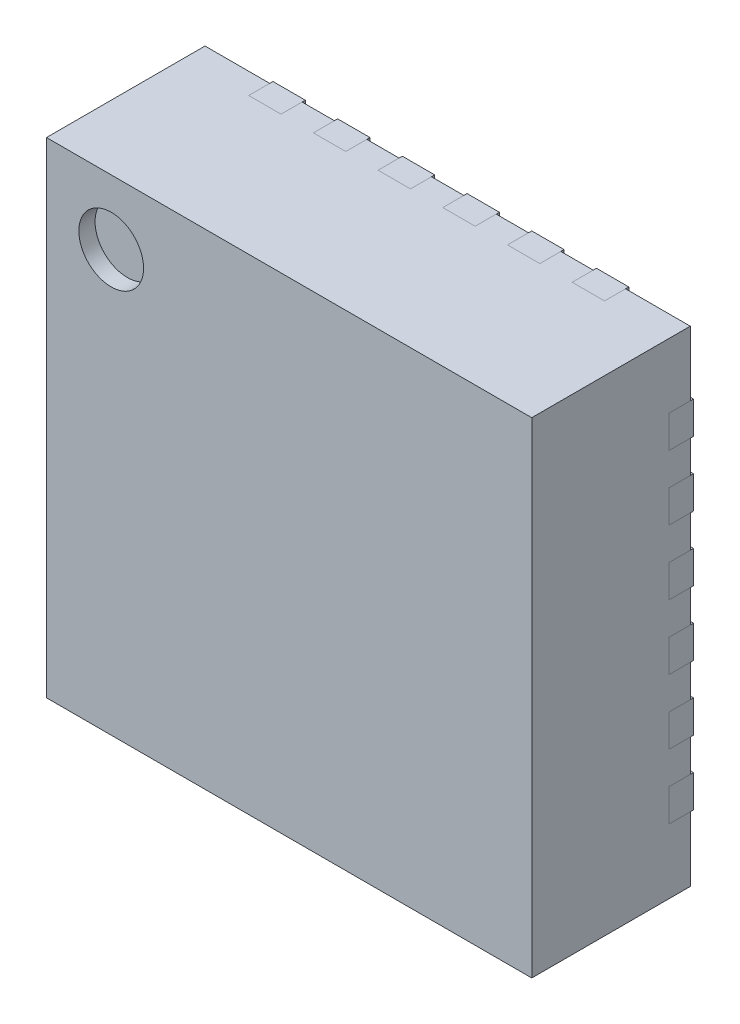
SolidWorks part; units mm, degrees
ref_plane "Plan de face" through (0, 0, 0) normal (0, 0, 1) x (1, 0, 0)
ref_plane "Plan de dessus" through (0, 0, 0) normal (0, 1, 0) x (1, 0, 0)
ref_plane "Plan de droite" through (0, 0, 0) normal (1, 0, 0) x (0, 0, -1)
sketch "Esquisse1" plane through (0, 0, 0) normal (0, 0, 1) x (1, 0, 0)
  line L1 (-1.5, 1.5) -> (1.5, 1.5)
  line L2 (-1.5, 1.5) -> (-1.5, -1.5)
  line L3 (-1.5, -1.5) -> (1.5, -1.5)
  line L4 (1.5, 1.5) -> (1.5, -1.5)
  line L5 (-1.5, 1.5) -> (1.5, -1.5) construction
  line L6 (-1.5, -1.5) -> (1.5, 1.5) construction
  point P0 (0, 0)
  dimension "D1" = 3
  dimension "D2" = 3
extrude "Boss.-Extru.1" add sketch "Esquisse1" along normal blind 0.98
sketch "Esquisse3" plane through (0, 0, 0) normal (0, 0, 1) x (1, 0, 0)
  line L0 (-1.275, -0.5) -> (-1.5, -0.5)
  line L1 (-1.5, -0.5) -> (-1.5, -0.7)
  line L2 (-1.7498, -0.6) -> (-1.1482, -0.6) construction
  line L4 (-1.5, 1.5) -> (-1.5, -1.5) construction
  line L5 (-1.2, -0.575) -> (-1.2, -0.625)
  line L9 (0.85, 0.62) -> (0.85, -0.62)
  line L10 (0.7, -0.77) -> (-0.7, -0.77)
  line L12 (1.8846, 0) -> (-2.1932, 0) construction
  line L13 (-1.5, 1.1) -> (-1.28, 1.1)
  line L26 (-1.7498, -1) -> (-1.1482, -1) construction
  line L60 (-1.5, -0.7) -> (-1.275, -0.7)
  line L77 (-1.5, -0.1) -> (-1.5, -0.3)
  line L78 (-0.6, 0.77) -> (-0.85, 0.52)
  line L79 (0.7, 0.77) -> (-0.6, 0.77)
  line L80 (-0.85, 0.52) -> (-0.85, -0.62)
  line L81 (-1.5, -0.3) -> (-1.275, -0.3)
  line L82 (-1.2, -0.175) -> (-1.2, -0.225)
  line L83 (-1.275, -0.1) -> (-1.5, -0.1)
  line L84 (-1.5, 0.3) -> (-1.5, 0.1)
  line L85 (-1.5, 0.1) -> (-1.275, 0.1)
  line L86 (-1.2, 0.225) -> (-1.2, 0.175)
  line L87 (-1.275, 0.3) -> (-1.5, 0.3)
  line L88 (-1.5, 0.7) -> (-1.5, 0.5)
  line L89 (-1.5, 0.5) -> (-1.275, 0.5)
  line L90 (-1.2, 0.625) -> (-1.2, 0.575)
  line L91 (-1.275, 0.7) -> (-1.5, 0.7)
  line L92 (-1.5, -1.5) -> (1.5, -1.5) construction
  line L93 (-1.5, -0.9) -> (-1.5, -1.1)
  line L94 (-1.5, -1.1) -> (-1.28, -1.1)
  line L96 (-1.28, -0.9) -> (-1.5, -0.9)
  line L97 (0, 0) -> (-1.6613, -1.6613) construction
  line L98 (-1.28, 0.9) -> (-1.5, 0.9)
  line L99 (-1.5, 0.9) -> (-1.5, 1.1)
  line L115 (1.1, 1.5) -> (1.1, 1.28)
  line L116 (0.9, 1.5) -> (1.1, 1.5)
  line L117 (0.9, 1.28) -> (0.9, 1.5)
  line L118 (0.7, 1.5) -> (0.5, 1.5)
  line L119 (0.7, 1.275) -> (0.7, 1.5)
  line L135 (0.625, 1.2) -> (0.575, 1.2)
  line L136 (0.5, 1.5) -> (0.5, 1.275)
  line L137 (0.3, 1.5) -> (0.1, 1.5)
  line L138 (0.3, 1.275) -> (0.3, 1.5)
  line L139 (0.225, 1.2) -> (0.175, 1.2)
  line L155 (0.1, 1.5) -> (0.1, 1.275)
  line L156 (-0.1, 1.5) -> (-0.3, 1.5)
  line L157 (-0.1, 1.275) -> (-0.1, 1.5)
  line L158 (-0.175, 1.2) -> (-0.225, 1.2)
  line L159 (-0.3, 1.5) -> (-0.3, 1.275)
  line L160 (1.5, -1.1) -> (1.28, -1.1)
  line L161 (1.5, -0.9) -> (1.5, -1.1)
  line L162 (1.28, -0.9) -> (1.5, -0.9)
  line L163 (1.5, -0.7) -> (1.5, -0.5)
  line L164 (1.275, -0.7) -> (1.5, -0.7)
  line L165 (1.2, -0.625) -> (1.2, -0.575)
  line L166 (1.5, -0.5) -> (1.275, -0.5)
  line L167 (1.5, -0.3) -> (1.5, -0.1)
  line L168 (1.275, -0.3) -> (1.5, -0.3)
  line L169 (1.2, -0.225) -> (1.2, -0.175)
  line L170 (1.5, -0.1) -> (1.275, -0.1)
  line L171 (1.5, 0.1) -> (1.5, 0.3)
  line L172 (1.275, 0.1) -> (1.5, 0.1)
  line L173 (1.2, 0.175) -> (1.2, 0.225)
  line L174 (1.5, 0.3) -> (1.275, 0.3)
  line L175 (-1.1, -1.5) -> (-1.1, -1.28)
  line L176 (-0.9, -1.5) -> (-1.1, -1.5)
  line L177 (-0.9, -1.28) -> (-0.9, -1.5)
  line L178 (-0.7, -1.5) -> (-0.5, -1.5)
  line L179 (-0.7, -1.275) -> (-0.7, -1.5)
  line L180 (-0.625, -1.2) -> (-0.575, -1.2)
  line L181 (-0.5, -1.5) -> (-0.5, -1.275)
  line L182 (-0.3, -1.5) -> (-0.1, -1.5)
  line L183 (-0.3, -1.275) -> (-0.3, -1.5)
  line L184 (-0.225, -1.2) -> (-0.175, -1.2)
  line L185 (-0.1, -1.5) -> (-0.1, -1.275)
  line L186 (0.1, -1.5) -> (0.3, -1.5)
  line L187 (0.1, -1.275) -> (0.1, -1.5)
  line L188 (0.175, -1.2) -> (0.225, -1.2)
  line L189 (0.3, -1.5) -> (0.3, -1.275)
  line L190 (-0.5, 1.5) -> (-0.7, 1.5)
  line L191 (-0.5, 1.275) -> (-0.5, 1.5)
  line L192 (-0.7, 1.5) -> (-0.7, 1.275)
  line L193 (-0.575, 1.2) -> (-0.625, 1.2)
  line L194 (-0.9, 1.5) -> (-1.1, 1.5)
  line L195 (-0.9, 1.28) -> (-0.9, 1.5)
  line L196 (-1.1, 1.5) -> (-1.1, 1.28)
  line L197 (1.5, 0.5) -> (1.5, 0.7)
  line L198 (1.275, 0.5) -> (1.5, 0.5)
  line L199 (1.5, 0.7) -> (1.275, 0.7)
  line L200 (1.2, 0.575) -> (1.2, 0.625)
  line L201 (1.5, 0.9) -> (1.5, 1.1)
  line L202 (1.28, 0.9) -> (1.5, 0.9)
  line L203 (1.5, 1.1) -> (1.28, 1.1)
  line L204 (0.5, -1.5) -> (0.7, -1.5)
  line L205 (0.5, -1.275) -> (0.5, -1.5)
  line L206 (0.7, -1.5) -> (0.7, -1.275)
  line L207 (0.575, -1.2) -> (0.625, -1.2)
  line L208 (0.9, -1.5) -> (1.1, -1.5)
  line L209 (0.9, -1.28) -> (0.9, -1.5)
  line L210 (1.1, -1.5) -> (1.1, -1.28)
  arc A0 (-1.275, -0.7) -> (-1.2, -0.625) centre (-1.275, -0.625) ccw
  arc A1 (-1.275, -0.5) -> (-1.2, -0.575) centre (-1.275, -0.575) cw
  arc A2 (-0.7, -0.77) -> (-0.85, -0.62) centre (-0.7, -0.62) cw
  arc A3 (0.85, -0.62) -> (0.7, -0.77) centre (0.7, -0.62) cw
  arc A4 (0.7, 0.77) -> (0.85, 0.62) centre (0.7, 0.62) cw
  arc A35 (-1.275, -0.3) -> (-1.2, -0.225) centre (-1.275, -0.225) ccw
  arc A36 (-1.275, -0.1) -> (-1.2, -0.175) centre (-1.275, -0.175) cw
  arc A37 (-1.275, 0.1) -> (-1.2, 0.175) centre (-1.275, 0.175) ccw
  arc A38 (-1.275, 0.3) -> (-1.2, 0.225) centre (-1.275, 0.225) cw
  arc A39 (-1.275, 0.5) -> (-1.2, 0.575) centre (-1.275, 0.575) ccw
  arc A40 (-1.275, 0.7) -> (-1.2, 0.625) centre (-1.275, 0.625) cw
  arc A41 (-1.2, -0.98) -> (-1.28, -0.9) centre (-1.28, -0.98) ccw
  arc A43 (-1.28, -1.1) -> (-1.2, -0.98) centre (-1.3216, -0.9856) ccw
  arc A44 (-1.28, 1.1) -> (-1.2, 0.98) centre (-1.3216, 0.9856) cw
  arc A45 (-1.2, 0.98) -> (-1.28, 0.9) centre (-1.28, 0.98) cw
  arc A54 (1.1, 1.28) -> (0.98, 1.2) centre (0.9856, 1.3216) cw
  arc A55 (0.98, 1.2) -> (0.9, 1.28) centre (0.98, 1.28) cw
  arc A56 (0.7, 1.275) -> (0.625, 1.2) centre (0.625, 1.275) cw
  arc A57 (0.5, 1.275) -> (0.575, 1.2) centre (0.575, 1.275) ccw
  arc A66 (0.3, 1.275) -> (0.225, 1.2) centre (0.225, 1.275) cw
  arc A67 (0.1, 1.275) -> (0.175, 1.2) centre (0.175, 1.275) ccw
  arc A68 (-0.1, 1.275) -> (-0.175, 1.2) centre (-0.175, 1.275) cw
  arc A69 (-0.3, 1.275) -> (-0.225, 1.2) centre (-0.225, 1.275) ccw
  arc A78 (1.28, -1.1) -> (1.2, -0.98) centre (1.3216, -0.9856) cw
  arc A79 (1.2, -0.98) -> (1.28, -0.9) centre (1.28, -0.98) cw
  arc A80 (1.275, -0.7) -> (1.2, -0.625) centre (1.275, -0.625) cw
  arc A81 (1.275, -0.5) -> (1.2, -0.575) centre (1.275, -0.575) ccw
  arc A82 (1.275, -0.3) -> (1.2, -0.225) centre (1.275, -0.225) cw
  arc A83 (1.275, -0.1) -> (1.2, -0.175) centre (1.275, -0.175) ccw
  arc A84 (1.275, 0.1) -> (1.2, 0.175) centre (1.275, 0.175) cw
  arc A85 (1.275, 0.3) -> (1.2, 0.225) centre (1.275, 0.225) ccw
  arc A86 (-1.1, -1.28) -> (-0.98, -1.2) centre (-0.9856, -1.3216) cw
  arc A87 (-0.98, -1.2) -> (-0.9, -1.28) centre (-0.98, -1.28) cw
  arc A88 (-0.7, -1.275) -> (-0.625, -1.2) centre (-0.625, -1.275) cw
  arc A89 (-0.5, -1.275) -> (-0.575, -1.2) centre (-0.575, -1.275) ccw
  arc A90 (-0.3, -1.275) -> (-0.225, -1.2) centre (-0.225, -1.275) cw
  arc A91 (-0.1, -1.275) -> (-0.175, -1.2) centre (-0.175, -1.275) ccw
  arc A92 (0.1, -1.275) -> (0.175, -1.2) centre (0.175, -1.275) cw
  arc A93 (0.3, -1.275) -> (0.225, -1.2) centre (0.225, -1.275) ccw
  arc A94 (-0.5, 1.275) -> (-0.575, 1.2) centre (-0.575, 1.275) cw
  arc A95 (-0.7, 1.275) -> (-0.625, 1.2) centre (-0.625, 1.275) ccw
  arc A96 (-0.98, 1.2) -> (-0.9, 1.28) centre (-0.98, 1.28) ccw
  arc A97 (-1.1, 1.28) -> (-0.98, 1.2) centre (-0.9856, 1.3216) ccw
  arc A98 (1.275, 0.5) -> (1.2, 0.575) centre (1.275, 0.575) cw
  arc A99 (1.275, 0.7) -> (1.2, 0.625) centre (1.275, 0.625) ccw
  arc A100 (1.2, 0.98) -> (1.28, 0.9) centre (1.28, 0.98) ccw
  arc A101 (1.28, 1.1) -> (1.2, 0.98) centre (1.3216, 0.9856) ccw
  arc A102 (0.5, -1.275) -> (0.575, -1.2) centre (0.575, -1.275) cw
  arc A103 (0.7, -1.275) -> (0.625, -1.2) centre (0.625, -1.275) ccw
  arc A104 (0.98, -1.2) -> (0.9, -1.28) centre (0.98, -1.28) ccw
  arc A105 (1.1, -1.28) -> (0.98, -1.2) centre (0.9856, -1.3216) ccw
  point P13 (-1.2, -0.6)
  point P16 (-1.2, -0.6641)
  point P19 (-1.2, -0.5359)
  point P20 (0, 0)
  point P168 (0, 0)
  point P171 (0, 0)
  point P216 (0, 0)
  point P218 (0, 0)
  dimension "D1" = 0.075
  dimension "D7" = 0.15
  dimension "D13" = 0.08
  dimension "D14" = 0.77
  dimension "D16" = 0.85
  dimension "D17" = 0.1218
  dimension "D2" = 0.9
  dimension "D3" = 4
  dimension "D4" = 1.7
  dimension "D5" = 1.54
  dimension "D6" = 0.2
  dimension "D9" = 0
  dimension "D8" = 0.3
  dimension "D10" = 0.4
  dimension "D11" = 0.2
  dimension "D12" = 0.1
  dimension "D15" = 0.22
  dimension "D18" = 4
  dimension "D19" = 4
extrude "Enlèv. mat.-Extru.3" cut sketch "Esquisse3" along normal blind 0.13
sketch "Esquisse4" plane through (0, 0, 0) normal (0, 0, 1) x (1, 0, 0)
  line L0 (-1.275, -0.5) -> (-1.5, -0.5)
  line L1 (-1.5, -0.5) -> (-1.5, -0.7)
  line L2 (-1.7498, -0.6) -> (-1.1482, -0.6) construction
  line L5 (-1.2, -0.575) -> (-1.2, -0.625)
  line L9 (0.85, 0.62) -> (0.85, -0.62)
  line L10 (0.7, -0.77) -> (-0.7, -0.77)
  line L12 (1.8846, 0) -> (-2.1932, 0) construction
  line L13 (-1.5, 1.1) -> (-1.28, 1.1)
  line L26 (-1.7498, -1) -> (-1.1482, -1) construction
  line L60 (-1.5, -0.7) -> (-1.275, -0.7)
  line L77 (-1.5, -0.1) -> (-1.5, -0.3)
  line L78 (-0.6, 0.77) -> (-0.85, 0.52)
  line L79 (0.7, 0.77) -> (-0.6, 0.77)
  line L80 (-0.85, 0.52) -> (-0.85, -0.62)
  line L81 (-1.5, -0.3) -> (-1.275, -0.3)
  line L82 (-1.2, -0.175) -> (-1.2, -0.225)
  line L83 (-1.275, -0.1) -> (-1.5, -0.1)
  line L84 (-1.5, 0.3) -> (-1.5, 0.1)
  line L85 (-1.5, 0.1) -> (-1.275, 0.1)
  line L86 (-1.2, 0.225) -> (-1.2, 0.175)
  line L87 (-1.275, 0.3) -> (-1.5, 0.3)
  line L88 (-1.5, 0.7) -> (-1.5, 0.5)
  line L89 (-1.5, 0.5) -> (-1.275, 0.5)
  line L90 (-1.2, 0.625) -> (-1.2, 0.575)
  line L91 (-1.275, 0.7) -> (-1.5, 0.7)
  line L93 (-1.5, -0.9) -> (-1.5, -1.1)
  line L94 (-1.5, -1.1) -> (-1.28, -1.1)
  line L96 (-1.28, -0.9) -> (-1.5, -0.9)
  line L97 (0, 0) -> (-1.6613, -1.6613) construction
  line L98 (-1.28, 0.9) -> (-1.5, 0.9)
  line L99 (-1.5, 0.9) -> (-1.5, 1.1)
  line L115 (1.1, 1.5) -> (1.1, 1.28)
  line L116 (0.9, 1.5) -> (1.1, 1.5)
  line L117 (0.9, 1.28) -> (0.9, 1.5)
  line L118 (0.7, 1.5) -> (0.5, 1.5)
  line L119 (0.7, 1.275) -> (0.7, 1.5)
  line L135 (0.625, 1.2) -> (0.575, 1.2)
  line L136 (0.5, 1.5) -> (0.5, 1.275)
  line L137 (0.3, 1.5) -> (0.1, 1.5)
  line L138 (0.3, 1.275) -> (0.3, 1.5)
  line L139 (0.225, 1.2) -> (0.175, 1.2)
  line L155 (0.1, 1.5) -> (0.1, 1.275)
  line L156 (-0.1, 1.5) -> (-0.3, 1.5)
  line L157 (-0.1, 1.275) -> (-0.1, 1.5)
  line L158 (-0.175, 1.2) -> (-0.225, 1.2)
  line L159 (-0.3, 1.5) -> (-0.3, 1.275)
  line L160 (1.5, -1.1) -> (1.28, -1.1)
  line L161 (1.5, -0.9) -> (1.5, -1.1)
  line L162 (1.28, -0.9) -> (1.5, -0.9)
  line L163 (1.5, -0.7) -> (1.5, -0.5)
  line L164 (1.275, -0.7) -> (1.5, -0.7)
  line L165 (1.2, -0.625) -> (1.2, -0.575)
  line L166 (1.5, -0.5) -> (1.275, -0.5)
  line L167 (1.5, -0.3) -> (1.5, -0.1)
  line L168 (1.275, -0.3) -> (1.5, -0.3)
  line L169 (1.2, -0.225) -> (1.2, -0.175)
  line L170 (1.5, -0.1) -> (1.275, -0.1)
  line L171 (1.5, 0.1) -> (1.5, 0.3)
  line L172 (1.275, 0.1) -> (1.5, 0.1)
  line L173 (1.2, 0.175) -> (1.2, 0.225)
  line L174 (1.5, 0.3) -> (1.275, 0.3)
  line L175 (-1.1, -1.5) -> (-1.1, -1.28)
  line L176 (-0.9, -1.5) -> (-1.1, -1.5)
  line L177 (-0.9, -1.28) -> (-0.9, -1.5)
  line L178 (-0.7, -1.5) -> (-0.5, -1.5)
  line L179 (-0.7, -1.275) -> (-0.7, -1.5)
  line L180 (-0.625, -1.2) -> (-0.575, -1.2)
  line L181 (-0.5, -1.5) -> (-0.5, -1.275)
  line L182 (-0.3, -1.5) -> (-0.1, -1.5)
  line L183 (-0.3, -1.275) -> (-0.3, -1.5)
  line L184 (-0.225, -1.2) -> (-0.175, -1.2)
  line L185 (-0.1, -1.5) -> (-0.1, -1.275)
  line L186 (0.1, -1.5) -> (0.3, -1.5)
  line L187 (0.1, -1.275) -> (0.1, -1.5)
  line L188 (0.175, -1.2) -> (0.225, -1.2)
  line L189 (0.3, -1.5) -> (0.3, -1.275)
  line L190 (-0.5, 1.5) -> (-0.7, 1.5)
  line L191 (-0.5, 1.275) -> (-0.5, 1.5)
  line L192 (-0.7, 1.5) -> (-0.7, 1.275)
  line L193 (-0.575, 1.2) -> (-0.625, 1.2)
  line L194 (-0.9, 1.5) -> (-1.1, 1.5)
  line L195 (-0.9, 1.28) -> (-0.9, 1.5)
  line L196 (-1.1, 1.5) -> (-1.1, 1.28)
  line L197 (1.5, 0.5) -> (1.5, 0.7)
  line L198 (1.275, 0.5) -> (1.5, 0.5)
  line L199 (1.5, 0.7) -> (1.275, 0.7)
  line L200 (1.2, 0.575) -> (1.2, 0.625)
  line L201 (1.5, 0.9) -> (1.5, 1.1)
  line L202 (1.28, 0.9) -> (1.5, 0.9)
  line L203 (1.5, 1.1) -> (1.28, 1.1)
  line L204 (0.5, -1.5) -> (0.7, -1.5)
  line L205 (0.5, -1.275) -> (0.5, -1.5)
  line L206 (0.7, -1.5) -> (0.7, -1.275)
  line L207 (0.575, -1.2) -> (0.625, -1.2)
  line L208 (0.9, -1.5) -> (1.1, -1.5)
  line L209 (0.9, -1.28) -> (0.9, -1.5)
  line L210 (1.1, -1.5) -> (1.1, -1.28)
  arc A0 (-1.275, -0.7) -> (-1.2, -0.625) centre (-1.275, -0.625) ccw
  arc A1 (-1.275, -0.5) -> (-1.2, -0.575) centre (-1.275, -0.575) cw
  arc A2 (-0.7, -0.77) -> (-0.85, -0.62) centre (-0.7, -0.62) cw
  arc A3 (0.85, -0.62) -> (0.7, -0.77) centre (0.7, -0.62) cw
  arc A4 (0.7, 0.77) -> (0.85, 0.62) centre (0.7, 0.62) cw
  arc A35 (-1.275, -0.3) -> (-1.2, -0.225) centre (-1.275, -0.225) ccw
  arc A36 (-1.275, -0.1) -> (-1.2, -0.175) centre (-1.275, -0.175) cw
  arc A37 (-1.275, 0.1) -> (-1.2, 0.175) centre (-1.275, 0.175) ccw
  arc A38 (-1.275, 0.3) -> (-1.2, 0.225) centre (-1.275, 0.225) cw
  arc A39 (-1.275, 0.5) -> (-1.2, 0.575) centre (-1.275, 0.575) ccw
  arc A40 (-1.275, 0.7) -> (-1.2, 0.625) centre (-1.275, 0.625) cw
  arc A41 (-1.2, -0.98) -> (-1.28, -0.9) centre (-1.28, -0.98) ccw
  arc A43 (-1.28, -1.1) -> (-1.2, -0.98) centre (-1.3216, -0.9856) ccw
  arc A44 (-1.28, 1.1) -> (-1.2, 0.98) centre (-1.3216, 0.9856) cw
  arc A45 (-1.2, 0.98) -> (-1.28, 0.9) centre (-1.28, 0.98) cw
  arc A54 (1.1, 1.28) -> (0.98, 1.2) centre (0.9856, 1.3216) cw
  arc A55 (0.98, 1.2) -> (0.9, 1.28) centre (0.98, 1.28) cw
  arc A56 (0.7, 1.275) -> (0.625, 1.2) centre (0.625, 1.275) cw
  arc A57 (0.5, 1.275) -> (0.575, 1.2) centre (0.575, 1.275) ccw
  arc A66 (0.3, 1.275) -> (0.225, 1.2) centre (0.225, 1.275) cw
  arc A67 (0.1, 1.275) -> (0.175, 1.2) centre (0.175, 1.275) ccw
  arc A68 (-0.1, 1.275) -> (-0.175, 1.2) centre (-0.175, 1.275) cw
  arc A69 (-0.3, 1.275) -> (-0.225, 1.2) centre (-0.225, 1.275) ccw
  arc A78 (1.28, -1.1) -> (1.2, -0.98) centre (1.3216, -0.9856) cw
  arc A79 (1.2, -0.98) -> (1.28, -0.9) centre (1.28, -0.98) cw
  arc A80 (1.275, -0.7) -> (1.2, -0.625) centre (1.275, -0.625) cw
  arc A81 (1.275, -0.5) -> (1.2, -0.575) centre (1.275, -0.575) ccw
  arc A82 (1.275, -0.3) -> (1.2, -0.225) centre (1.275, -0.225) cw
  arc A83 (1.275, -0.1) -> (1.2, -0.175) centre (1.275, -0.175) ccw
  arc A84 (1.275, 0.1) -> (1.2, 0.175) centre (1.275, 0.175) cw
  arc A85 (1.275, 0.3) -> (1.2, 0.225) centre (1.275, 0.225) ccw
  arc A86 (-1.1, -1.28) -> (-0.98, -1.2) centre (-0.9856, -1.3216) cw
  arc A87 (-0.98, -1.2) -> (-0.9, -1.28) centre (-0.98, -1.28) cw
  arc A88 (-0.7, -1.275) -> (-0.625, -1.2) centre (-0.625, -1.275) cw
  arc A89 (-0.5, -1.275) -> (-0.575, -1.2) centre (-0.575, -1.275) ccw
  arc A90 (-0.3, -1.275) -> (-0.225, -1.2) centre (-0.225, -1.275) cw
  arc A91 (-0.1, -1.275) -> (-0.175, -1.2) centre (-0.175, -1.275) ccw
  arc A92 (0.1, -1.275) -> (0.175, -1.2) centre (0.175, -1.275) cw
  arc A93 (0.3, -1.275) -> (0.225, -1.2) centre (0.225, -1.275) ccw
  arc A94 (-0.5, 1.275) -> (-0.575, 1.2) centre (-0.575, 1.275) cw
  arc A95 (-0.7, 1.275) -> (-0.625, 1.2) centre (-0.625, 1.275) ccw
  arc A96 (-0.98, 1.2) -> (-0.9, 1.28) centre (-0.98, 1.28) ccw
  arc A97 (-1.1, 1.28) -> (-0.98, 1.2) centre (-0.9856, 1.3216) ccw
  arc A98 (1.275, 0.5) -> (1.2, 0.575) centre (1.275, 0.575) cw
  arc A99 (1.275, 0.7) -> (1.2, 0.625) centre (1.275, 0.625) ccw
  arc A100 (1.2, 0.98) -> (1.28, 0.9) centre (1.28, 0.98) ccw
  arc A101 (1.28, 1.1) -> (1.2, 0.98) centre (1.3216, 0.9856) ccw
  arc A102 (0.5, -1.275) -> (0.575, -1.2) centre (0.575, -1.275) cw
  arc A103 (0.7, -1.275) -> (0.625, -1.2) centre (0.625, -1.275) ccw
  arc A104 (0.98, -1.2) -> (0.9, -1.28) centre (0.98, -1.28) ccw
  arc A105 (1.1, -1.28) -> (0.98, -1.2) centre (0.9856, -1.3216) ccw
  point P13 (-1.2, -0.6)
  point P16 (-1.2, -0.6641)
  point P19 (-1.2, -0.5359)
  point P20 (0, 0)
  point P168 (0, 0)
  point P171 (0, 0)
  point P216 (0, 0)
  point P218 (0, 0)
  dimension "D1" = 0.075
  dimension "D7" = 0.15
  dimension "D13" = 0.08
  dimension "D14" = 0.77
  dimension "D16" = 0.85
  dimension "D17" = 0.1218
  dimension "D3" = 4
  dimension "D4" = 1.7
  dimension "D5" = 1.54
  dimension "D6" = 0.2
  dimension "D8" = 0.3
  dimension "D10" = 0.4
  dimension "D11" = 0.2
  dimension "D12" = 0.1
  dimension "D15" = 0.22
  dimension "D18" = 4
  dimension "D19" = 4
extrude "Boss.-Extru.3" add sketch "Esquisse4" along normal blind 0.13 and the other way blind 0.02 separate body
sketch "Esquisse5" plane through (0, 0, 0.98) normal (0, 0, 1) x (1, 0, 0)
  line L0 (1.5, 1.5) -> (-1.5, 1.5) construction
  line L1 (-1.5, 1.5) -> (-1.5, -1.5) construction
  circle A0 centre (-1.1, 1.1) radius 0.2
  dimension "D1" = 0.4
  dimension "D2" = 0.4
  dimension "D3" = 0.4
extrude "Enlèv. mat.-Extru.4" cut sketch "Esquisse5" against normal blind 0.1
